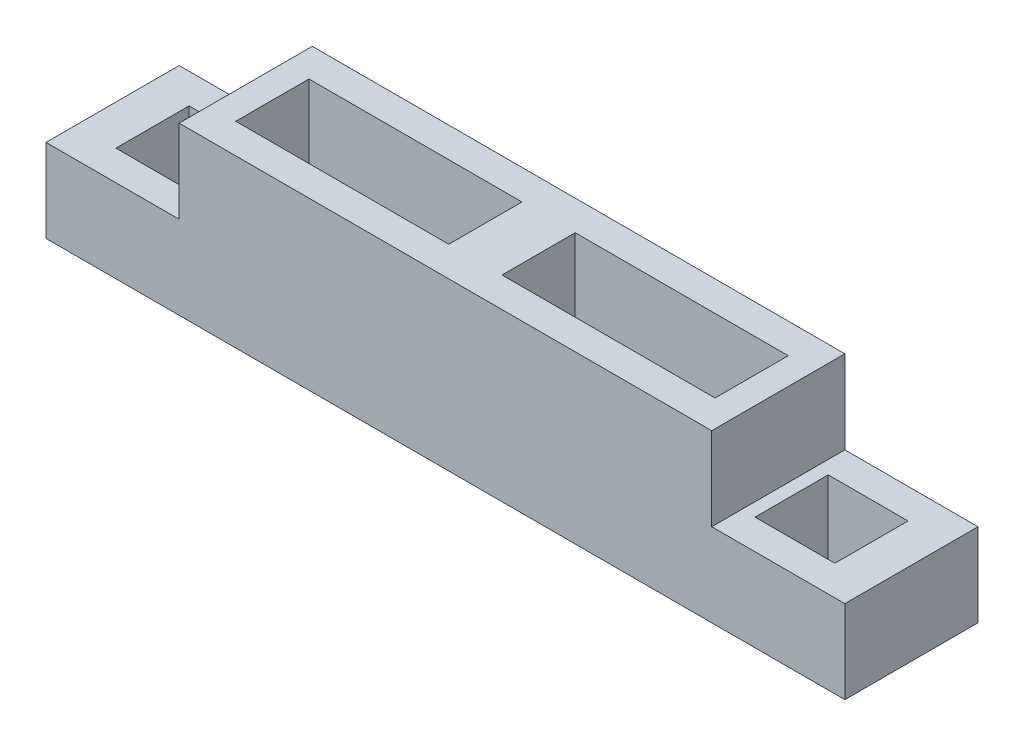
SolidWorks part; units mm, degrees
ref_plane "Спереди" through (0, 0, 0) normal (0, 0, 1) x (1, 0, 0)
ref_plane "Сверху" through (0, 0, 0) normal (0, 1, 0) x (1, 0, 0)
ref_plane "Справа" through (0, 0, 0) normal (1, 0, 0) x (0, 0, -1)
sketch "Эскиз1" plane through (0, 0, 0) normal (0, 1, 0) x (1, 0, 0)
  line L0 (-597.6403, 0) -> (621.3659, 0) construction
  line L1 (-600, 100) -> (600, 100)
  line L2 (-600, 100) -> (-600, -100)
  line L3 (-600, -100) -> (600, -100)
  line L4 (600, 100) -> (600, -100)
  line L5 (-600, 100) -> (600, -100) construction
  line L6 (-600, -100) -> (600, 100) construction
  line L7 (0, 184.918) -> (0, -165.1618) construction
  line L8 (360, -55) -> (40, 55) construction
  line L9 (-540, 55) -> (-420, 55)
  line L10 (-540, 55) -> (-540, -55)
  line L11 (-540, -55) -> (-420, -55)
  line L12 (-420, 55) -> (-420, -55)
  line L13 (-540, 55) -> (-420, -55) construction
  line L14 (-540, -55) -> (-420, 55) construction
  line L15 (-360, 55) -> (-40, 55)
  line L16 (-360, 55) -> (-360, -55)
  line L17 (-360, -55) -> (-40, -55)
  line L18 (-40, 55) -> (-40, -55)
  line L19 (-360, 55) -> (-40, -55) construction
  line L20 (-360, -55) -> (-40, 55) construction
  line L21 (360, 55) -> (40, -55) construction
  line L22 (540, -55) -> (420, 55) construction
  line L23 (540, 55) -> (420, -55) construction
  line L24 (40, 55) -> (40, -55)
  line L25 (360, -55) -> (40, -55)
  line L26 (360, 55) -> (360, -55)
  line L27 (360, 55) -> (40, 55)
  line L28 (420, 55) -> (420, -55)
  line L29 (540, -55) -> (420, -55)
  line L30 (540, 55) -> (540, -55)
  line L31 (540, 55) -> (420, 55)
  point P0 (0, 0)
  point P10 (-480, 0)
  point P15 (0, 0)
  point P16 (-200, 0)
  point P29 (200, 0)
  point P30 (480, 0)
  point P31 (0, 0)
  point P32 (0, 0)
  point P33 (0, 0)
  point P34 (0, 0)
extrude "Бобышка-Вытянуть1" add sketch "Эскиз1" along normal blind 250
sketch "Эскиз2" plane through (0, 0, 100) normal (0, 0, 1) x (1, 0, 0)
  line L0 (0, 321.4699) -> (0, -92.9376) construction
  line L1 (-600, 250) -> (-400, 250)
  line L2 (-600, 250) -> (-600, 125)
  line L3 (-600, 125) -> (-400, 125)
  line L4 (-400, 250) -> (-400, 125)
  line L5 (400, 250) -> (400, 125)
  line L6 (600, 125) -> (400, 125)
  line L7 (600, 250) -> (600, 125)
  line L8 (600, 250) -> (400, 250)
extrude "Вырез-Вытянуть1" cut sketch "Эскиз2" against normal through all
